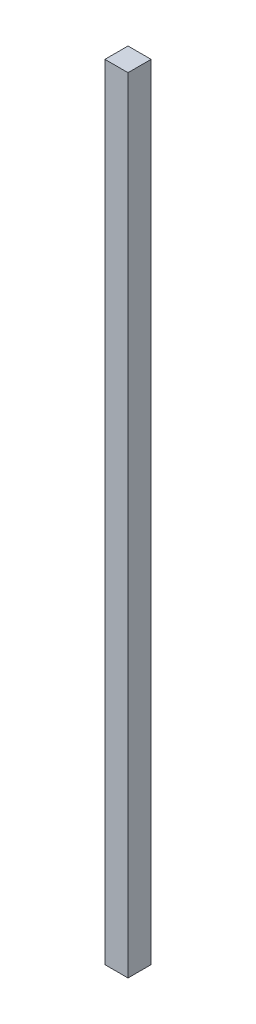
SolidWorks part; units mm, degrees
ref_plane "Front Plane" through (0, 0, 0) normal (0, 0, 1) x (1, 0, 0)
ref_plane "Top Plane" through (0, 0, 0) normal (0, 1, 0) x (1, 0, 0)
ref_plane "Right Plane" through (0, 0, 0) normal (1, 0, 0) x (0, 0, -1)
sketch "Sketch1" plane through (0, 0, 0) normal (0, 1, 0) x (1, 0, 0)
  line L1 (0, 0) -> (19.05, 0)
  line L2 (0, 0) -> (0, -19.05)
  line L3 (0, -19.05) -> (19.05, -19.05)
  line L4 (19.05, 0) -> (19.05, -19.05)
  dimension "D1" = 19.05
  dimension "D2" = 19.05
extrude "Boss-Extrude1" add sketch "Sketch1" along normal blind 647
